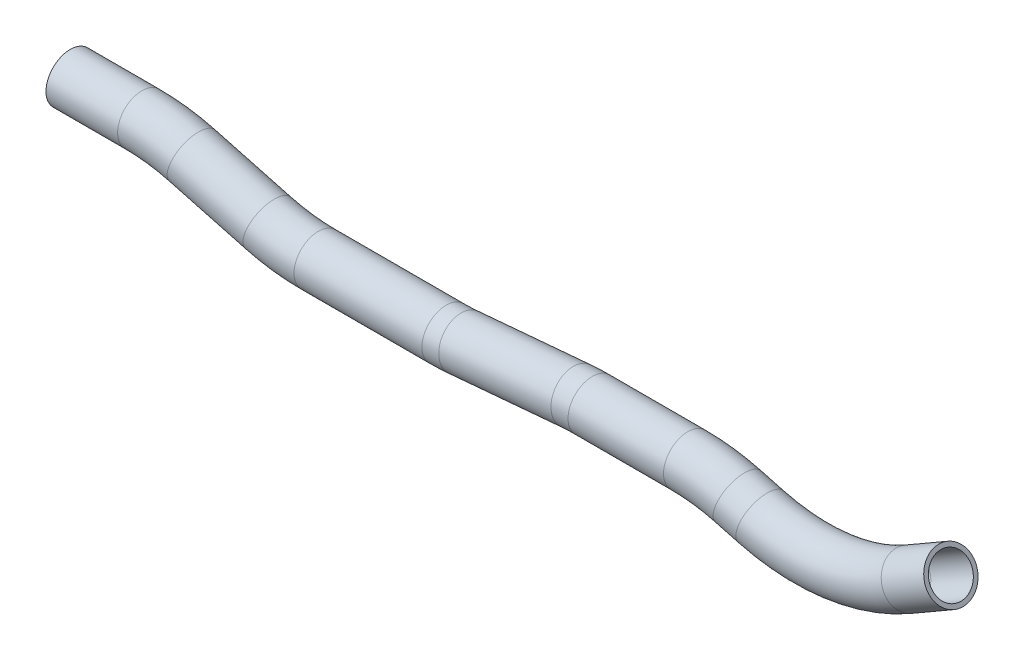
SolidWorks part; units mm, degrees
ref_plane "Front Plane" through (0, 0, 0) normal (0, 0, 1) x (1, 0, 0)
ref_plane "Top Plane" through (0, 0, 0) normal (0, 1, 0) x (1, 0, 0)
ref_plane "Right Plane" through (0, 0, 0) normal (1, 0, 0) x (0, 0, -1)
sketch "Sketch1" plane through (0, 0, 0) normal (0, 0, 1) x (1, 0, 0)
  line L0 (124.1817, -15.9493) -> (152.2498, -15.9493)
  line L1 (171.9718, -18.5458) -> (201.6606, -26.5009)
  line L2 (221.3826, -29.0973) -> (271.5238, -29.0973)
  line L3 (278.165, -28.8074) -> (322.1431, -24.9598)
  line L4 (124.1817, -15.9493) -> (199.7062, -15.9493) construction
  line L5 (201.6606, -26.5009) -> (171.9718, -18.5458) construction
  line L6 (171.9718, -18.5458) -> (71.2195, 8.4507) construction
  line L7 (171.9718, -18.5458) -> (201.6606, -26.5009) construction
  line L8 (201.6606, -26.5009) -> (258.6025, -41.7584) construction
  line L9 (271.5238, -29.0973) -> (221.3826, -29.0973) construction
  line L10 (221.3826, -29.0973) -> (122.1793, -29.0973) construction
  line L11 (221.3826, -29.0973) -> (271.5238, -29.0973) construction
  line L12 (322.1431, -24.9598) -> (278.165, -28.8074) construction
  line L13 (221.3826, -29.0973) -> (271.5238, -29.0973) construction
  line L14 (271.5238, -29.0973) -> (384.0117, -29.0973) construction
  line L16 (278.165, -28.8074) -> (209.5312, -34.812) construction
  line L17 (328.7844, -24.6698) -> (366.2255, -24.6698)
  line L18 (385.9475, -27.2663) -> (394.8389, -29.6487)
  line L20 (278.165, -28.8074) -> (322.1431, -24.9598) construction
  line L21 (322.1431, -24.9598) -> (411.1367, -17.1739) construction
  line L22 (366.2255, -24.6698) -> (328.7844, -24.6698) construction
  line L23 (328.7844, -24.6698) -> (188.7458, -24.6698) construction
  line L24 (328.7844, -24.6698) -> (366.2255, -24.6698) construction
  line L25 (366.2255, -24.6698) -> (457.8217, -24.6698) construction
  line L26 (394.8389, -29.6487) -> (385.9475, -27.2663) construction
  line L27 (385.9475, -27.2663) -> (250.8056, 8.9449) construction
  line L28 (385.9475, -27.2663) -> (394.8389, -29.6487) construction
  line L29 (394.8389, -29.6487) -> (645.3118, -96.7627) construction
  line L30 (452.6609, -22.0363) -> (469.3205, -12.4178)
  line L31 (469.3205, -12.4178) -> (292.9878, -114.2236) construction
  arc A0 (152.2498, -15.9493) -> (171.9718, -18.5458) centre (152.2498, -92.1493) cw
  arc A1 (201.6606, -26.5009) -> (221.3826, -29.0973) centre (221.3826, 47.1027) ccw
  arc A2 (271.5238, -29.0973) -> (278.165, -28.8074) centre (271.5238, 47.1027) ccw
  arc A3 (322.1431, -24.9598) -> (328.7844, -24.6698) centre (328.7844, -100.8698) cw
  arc A4 (366.2255, -24.6698) -> (385.9475, -27.2663) centre (366.2255, -100.8698) cw
  arc A5 (394.8389, -29.6487) -> (452.6609, -22.0363) centre (414.5609, 43.9548) ccw
  point P10 (274.8507, -29.0973)
  point P18 (211.3507, -29.0973)
  point P19 (162.2817, -15.9493)
  point P25 (325.4574, -24.6698)
  point P31 (425.3264, -37.8178)
  point P37 (376.2574, -24.6698)
  dimension "D3" = 76.2
  dimension "D6" = 76.2
  dimension "D9" = 63.5
  dimension "D8" = 76.2
  dimension "D10" = 76.2
  dimension "D12" = 76.2
  dimension "D13" = 76.2
  dimension "D1" = 38.1
  dimension "D2" = 15
  dimension "D4" = 50.8
  dimension "D5" = 15
  dimension "D7" = 5
  dimension "D11" = 5
  dimension "D14" = 50.8
  dimension "D15" = 50.8
  dimension "D16" = 15
  dimension "D17" = 45
  dimension "D18" = 50.8
  dimension "D19" = 50.8
ref_plane "Plane1" through (124.1817, -15.9493, 0) normal (1, 0, 0) x (0, 0, -1)
sketch "Sketch2" plane through (124.1817, -15.9493, 0) normal (1, 0, 0) x (0, 0, -1)
  circle A0 centre (0, 0) radius 9.525
  circle A1 centre (0, 0) radius 7.874
  dimension "D1" = 15.748
  dimension "D2" = 19.05
sweep "Sweep1" add profiles "Sketch2" path "Sketch1"
